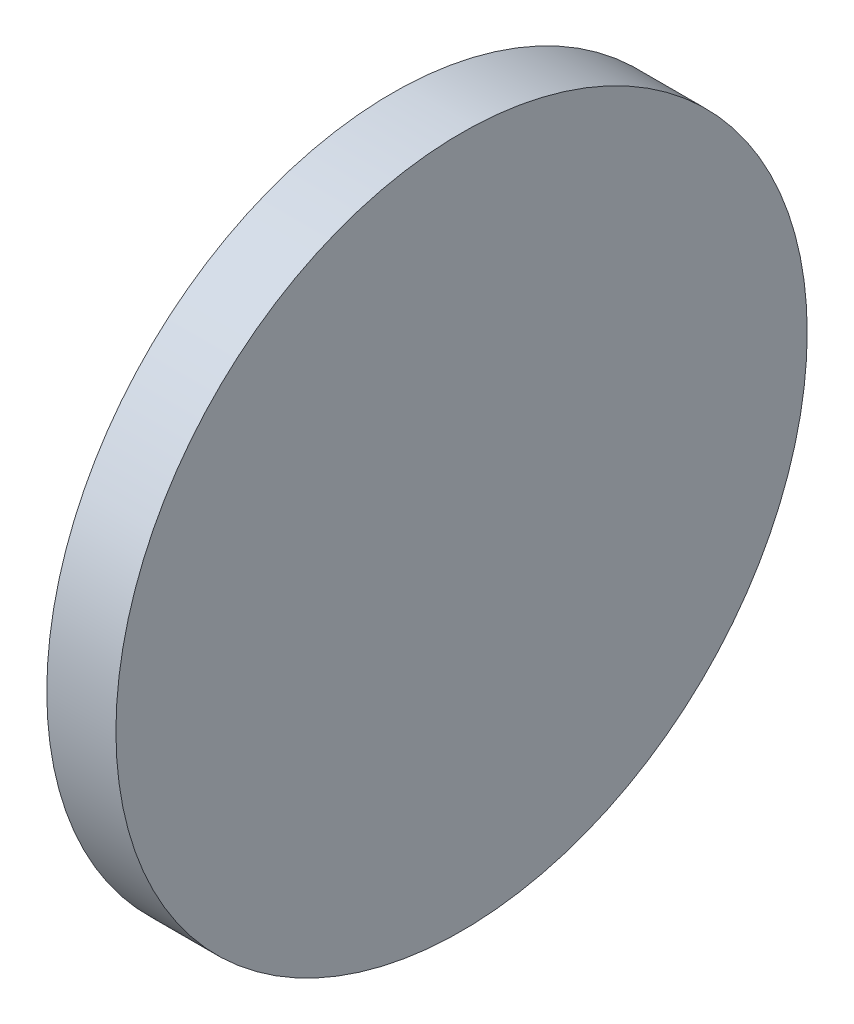
SolidWorks part; units mm, degrees
ref_plane "前视基准面" through (0, 0, 0) normal (0, 0, 1) x (1, 0, 0)
ref_plane "上视基准面" through (0, 0, 0) normal (0, 1, 0) x (1, 0, 0)
ref_plane "右视基准面" through (0, 0, 0) normal (1, 0, 0) x (0, 0, -1)
sketch "草图1" plane through (0, 0, 0) normal (0, 0, 1) x (1, 0, 0)
  line L0 (169.3339, 51.5288) -> (179.3693, 51.5288) construction
  line L1 (173.4187, 51.5288) -> (173.4187, 61.5288)
  line L2 (175.4187, 51.5288) -> (175.4187, 61.5288)
  line L3 (173.4187, 61.5288) -> (175.4187, 61.5288)
  line L4 (173.4187, 51.5288) -> (175.4187, 51.5288)
  dimension "D1" = 2
  dimension "D2" = 10
revolve "旋转1" add sketch "草图1" angle 360 about L0
